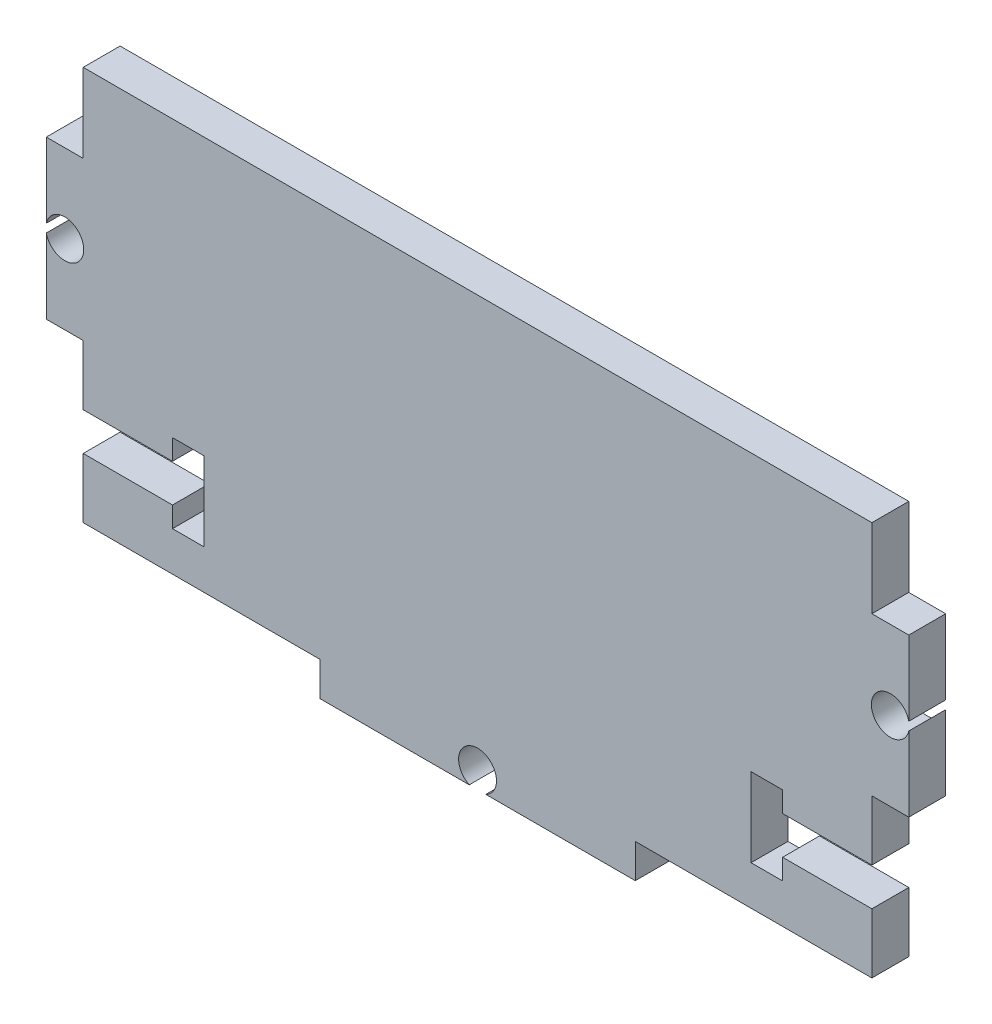
SolidWorks part; units mm, degrees
ref_plane "Front Plane" through (0, 0, 0) normal (0, 0, 1) x (1, 0, 0)
ref_plane "Top Plane" through (0, 0, 0) normal (0, 1, 0) x (1, 0, 0)
ref_plane "Right Plane" through (0, 0, 0) normal (1, 0, 0) x (0, 0, -1)
sketch "Sketch1" plane through (0, 0, 0) normal (0, 0, 1) x (1, 0, 0)
  line L0 (0, -55) -> (0, 55) construction
  line L1 (-31.75, -15.875) -> (31.75, -15.875)
  line L2 (-31.75, -15.875) -> (-31.75, 15.875)
  line L3 (-31.75, 15.875) -> (31.75, 15.875)
  line L4 (31.75, -15.875) -> (31.75, 15.875)
  line L5 (-31.75, -15.875) -> (31.75, 15.875) construction
  line L6 (-31.75, 15.875) -> (31.75, -15.875) construction
  line L7 (-31.75, 15.875) -> (-34.7218, 15.875)
  line L8 (-31.75, 15.875) -> (-31.75, 9.525)
  line L9 (-31.75, 9.525) -> (-34.7218, 9.525)
  line L10 (-34.7218, 15.875) -> (-34.7218, 9.525)
  line L11 (-31.75, -15.875) -> (-34.7218, -15.875)
  line L12 (-31.75, -15.875) -> (-31.75, -3.175)
  line L13 (-31.75, -3.175) -> (-34.7218, -3.175)
  line L14 (-34.7218, -15.875) -> (-34.7218, -3.175)
  line L15 (31.75, -3.175) -> (34.7218, -3.175)
  line L16 (34.7218, -15.875) -> (34.7218, -3.175)
  line L17 (31.75, -15.875) -> (34.7218, -15.875)
  line L18 (31.75, -15.875) -> (31.75, -3.175)
  line L19 (31.75, 9.525) -> (34.7218, 9.525)
  line L20 (34.7218, 15.875) -> (34.7218, 9.525)
  line L21 (31.75, 15.875) -> (34.7218, 15.875)
  line L22 (31.75, 15.875) -> (31.75, 9.525)
  line L23 (-34.7218, 9.525) -> (-34.7218, -3.175)
  line L24 (34.7218, 9.525) -> (34.7218, -3.175)
  line L25 (-34.7218, 9.525) -> (-34.7218, -3.175)
  line L27 (-12.7, -15.875) -> (12.7, -15.875)
  line L28 (-12.7, -15.875) -> (-12.7, -18.6147)
  line L29 (-12.7, -18.6147) -> (12.7, -18.6147)
  line L30 (12.7, -15.875) -> (12.7, -18.6147)
  point P0 (0, 0)
  point P24 (0, -15.875)
  point P25 (0, -18.6147)
  dimension "D1" = 63.5
  dimension "D2" = 31.75
  dimension "D3" = 12.7
  dimension "D4" = 2.9718
  dimension "D5" = 12.7
  dimension "D6" = 25.4
extrude "Boss-Extrude1" add sketch "Sketch1" along normal blind 2.9718 contours L9 L23 L13 L2 | L1 L4 L3 L2 | L24 L19 L4 L15 | L30 L1 L28 L29
sketch "Sketch2" plane through (0, 0, 0) normal (0, 0, -1) x (-1, 0, 0)
  line L0 (-33.2359, -3.175) -> (-33.2359, 9.525) construction
  line L1 (-31.75, -3.175) -> (-34.7218, -3.175) construction
  line L2 (-31.75, 9.525) -> (-34.7218, 9.525) construction
  line L3 (-12.7, -17.2449) -> (12.7, -17.2449) construction
  line L4 (-12.7, -15.875) -> (-12.7, -18.6147) construction
  line L5 (12.7, -15.875) -> (12.7, -18.6147) construction
  line L6 (33.2359, -3.175) -> (33.2359, 9.525) construction
  line L7 (31.75, -3.175) -> (34.7218, -3.175) construction
  line L8 (31.75, 9.525) -> (34.7218, 9.525) construction
  line L9 (31.75, -9.525) -> (22.0218, -9.525) construction
  line L10 (31.75, -15.875) -> (31.75, -3.175) construction
  line L11 (22.0218, -12.7) -> (22.0218, -6.35)
  line L12 (34.7218, 9.525) -> (34.7218, -3.175) construction
  line L13 (0, 1.6345) -> (0, -1.6345) construction
  line L14 (-31.75, -11.049) -> (-31.75, -8.001)
  line L15 (-31.75, -11.049) -> (-24.5618, -11.049)
  line L16 (-24.5618, -12.7) -> (-24.5618, -11.049)
  line L17 (-22.0218, -12.7) -> (-24.5618, -12.7)
  line L18 (-22.0218, -12.7) -> (-22.0218, -6.35)
  line L19 (-22.0218, -6.35) -> (-24.5618, -6.35)
  line L20 (-24.5618, -8.001) -> (-24.5618, -6.35)
  line L21 (-31.75, -8.001) -> (-24.5618, -8.001)
  line L29 (31.75, -8.001) -> (24.5618, -8.001)
  line L30 (31.75, -11.049) -> (24.5618, -11.049)
  line L31 (24.5618, -12.7) -> (24.5618, -11.049)
  line L32 (22.0218, -12.7) -> (24.5618, -12.7)
  line L33 (31.75, -11.049) -> (31.75, -8.001)
  line L34 (22.0218, -6.35) -> (24.5618, -6.35)
  line L35 (24.5618, -8.001) -> (24.5618, -6.35)
  line L37 (24.5618, -12.7) -> (24.5618, -6.35) construction
  line L38 (31.75, -11.049) -> (22.0218, -11.049) construction
  line L39 (31.75, -8.001) -> (22.0218, -8.001) construction
  circle A0 centre (0, -17.2449) radius 1.524
  circle A1 centre (33.2359, 3.175) radius 1.524
  circle A2 centre (-33.2359, 3.175) radius 1.524
  point P31 (22.0218, -9.525)
  point P51 (0, 0)
  point P52 (-33.2359, 3.175)
  line M16 (-34.7218, 9.525) -> (-34.7218, -3.175)
  line M18 (-31.75, -3.175) -> (-31.75, -15.875)
  line M21 (-12.7, -18.6147) -> (12.7, -18.6147)
  line M26 (34.7218, -3.175) -> (34.7218, 9.525)
  dimension "D1" = 3.048
  dimension "D2" = 12.7
  dimension "D3" = 6.35
  dimension "D4" = 1.524
  dimension "D5" = 1.524
  dimension "D6" = 2.54
extrude "Cut-Extrude1" cut sketch "Sketch2" against normal through all contours A1 M26 | A2 M16 | L21 L15 L16 L17 L18 L19 L20 M18 | A0 M21 | L30 L31 L32 L11 L34 L35 L29 L33
